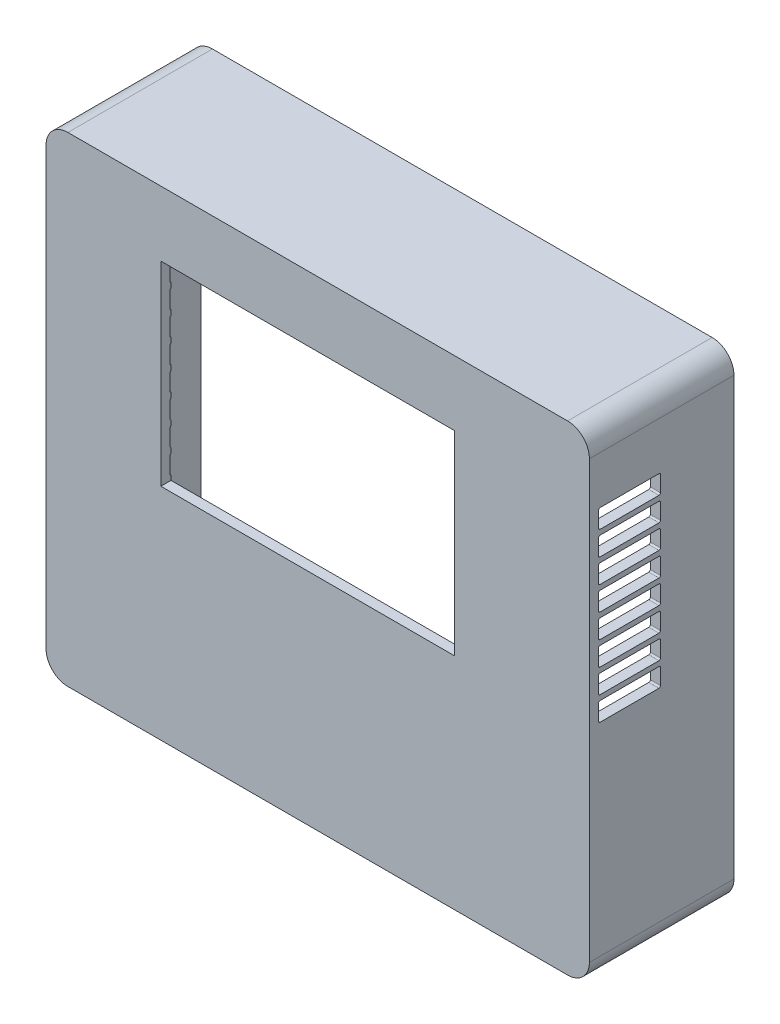
SolidWorks part; units mm, degrees
ref_plane "Front Plane" through (0, 0, 0) normal (0, 0, 1) x (1, 0, 0)
ref_plane "Top Plane" through (0, 0, 0) normal (0, 1, 0) x (1, 0, 0)
ref_plane "Right Plane" through (0, 0, 0) normal (1, 0, 0) x (0, 0, -1)
sketch "Sketch1" plane through (0, 0, 0) normal (0, 0, 1) x (1, 0, 0)
  line L4 (84, 51.09) -> (-14.4, 51.09)
  line L5 (-18.7, 46.79) -> (-18.7, -39.11)
  line L6 (-14.4, -43.41) -> (84, -43.41)
  line L7 (88.3, -39.11) -> (88.3, 46.79)
  line L8 (84, 51.09) -> (-14.4, 51.09)
  line L9 (-18.7, 46.79) -> (-18.7, -39.11)
  line L10 (-14.4, -43.41) -> (84, -43.41)
  line L11 (88.3, -39.11) -> (88.3, 46.79)
  line L12 (61.7, -0.1) -> (61.7, 38.3)
  line L13 (61.7, 38.3) -> (3.9, 38.3)
  line L14 (3.9, 38.3) -> (3.9, -0.1)
  line L15 (3.9, -0.1) -> (61.7, -0.1)
  line L16 (61.7, -0.1) -> (61.7, 38.3)
  line L17 (61.7, 38.3) -> (3.9, 38.3)
  line L18 (3.9, 38.3) -> (3.9, -0.1)
  line L19 (3.9, -0.1) -> (61.7, -0.1)
  arc A4 (88.3, 46.79) -> (84, 51.09) centre (84, 46.79) ccw
  arc A5 (-14.4, 51.09) -> (-18.7, 46.79) centre (-14.4, 46.79) ccw
  arc A6 (-18.7, -39.11) -> (-14.4, -43.41) centre (-14.4, -39.11) ccw
  arc A7 (84, -43.41) -> (88.3, -39.11) centre (84, -39.11) ccw
  arc A8 (88.3, 46.79) -> (84, 51.09) centre (84, 46.79) ccw
  arc A9 (-14.4, 51.09) -> (-18.7, 46.79) centre (-14.4, 46.79) ccw
  arc A10 (-18.7, -39.11) -> (-14.4, -43.41) centre (-14.4, -39.11) ccw
  arc A11 (84, -43.41) -> (88.3, -39.11) centre (84, -39.11) ccw
  dimension "D1" = 0
  dimension "D2" = 0
extrude "Boss-Extrude2" add sketch "Sketch1" against normal blind 2
sketch "Sketch2" plane through (0, 0, 0) normal (0, 0, 1) x (1, 0, 0)
  line L4 (84, 51.09) -> (-14.4, 51.09)
  line L5 (-18.7, 46.79) -> (-18.7, -39.11)
  line L6 (-14.4, -43.41) -> (84, -43.41)
  line L7 (88.3, -39.11) -> (88.3, 46.79)
  line L8 (84, 51.09) -> (-14.4, 51.09)
  line L9 (-18.7, 46.79) -> (-18.7, -39.11)
  line L10 (-14.4, -43.41) -> (84, -43.41)
  line L11 (88.3, -39.11) -> (88.3, 46.79)
  line L16 (84, 49.09) -> (-14.4, 49.09)
  line L17 (-16.7, 46.79) -> (-16.7, -39.11)
  line L18 (-14.4, -41.41) -> (84, -41.41)
  line L19 (86.3, -39.11) -> (86.3, 46.79)
  line L20 (84, 49.09) -> (-14.4, 49.09)
  line L21 (-16.7, 46.79) -> (-16.7, -39.11)
  line L22 (-14.4, -41.41) -> (84, -41.41)
  line L23 (86.3, -39.11) -> (86.3, 46.79)
  arc A4 (88.3, 46.79) -> (84, 51.09) centre (84, 46.79) ccw
  arc A5 (-14.4, 51.09) -> (-18.7, 46.79) centre (-14.4, 46.79) ccw
  arc A6 (-18.7, -39.11) -> (-14.4, -43.41) centre (-14.4, -39.11) ccw
  arc A7 (84, -43.41) -> (88.3, -39.11) centre (84, -39.11) ccw
  arc A8 (88.3, 46.79) -> (84, 51.09) centre (84, 46.79) ccw
  arc A9 (-14.4, 51.09) -> (-18.7, 46.79) centre (-14.4, 46.79) ccw
  arc A10 (-18.7, -39.11) -> (-14.4, -43.41) centre (-14.4, -39.11) ccw
  arc A11 (84, -43.41) -> (88.3, -39.11) centre (84, -39.11) ccw
  arc A16 (86.3, 46.79) -> (84, 49.09) centre (84, 46.79) ccw
  arc A17 (-14.4, 49.09) -> (-16.7, 46.79) centre (-14.4, 46.79) ccw
  arc A18 (-16.7, -39.11) -> (-14.4, -41.41) centre (-14.4, -39.11) ccw
  arc A19 (84, -41.41) -> (86.3, -39.11) centre (84, -39.11) ccw
  arc A20 (86.3, 46.79) -> (84, 49.09) centre (84, 46.79) ccw
  arc A21 (-14.4, 49.09) -> (-16.7, 46.79) centre (-14.4, 46.79) ccw
  arc A22 (-16.7, -39.11) -> (-14.4, -41.41) centre (-14.4, -39.11) ccw
  arc A23 (84, -41.41) -> (86.3, -39.11) centre (84, -39.11) ccw
  dimension "D1" = 0
  dimension "D2" = 2
extrude "Boss-Extrude3" add sketch "Sketch2" against normal up to surface (28.466 mm away)
sketch "Sketch4" plane through (0, -43.41, 0) normal (0, -1, 0) x (1, 0, 0)
  line L0 (68.12, -28.296) -> (69.827, -28.296) construction
  line L1 (69.827, -28.296) -> (69.827, -14.646) construction
  line L2 (69.827, -14.646) -> (68.12, -14.646) construction
  line L3 (66.12, -28.296) -> (68.12, -28.296) construction
  line L4 (-13.85, -17.296) -> (-13.85, -28.296)
  line L5 (-13.85, -28.296) -> (-4.55, -28.296)
  line L6 (-4.55, -28.296) -> (-4.55, -17.296)
  line L7 (-4.55, -17.296) -> (-13.85, -17.296)
  line L8 (-13.85, -17.296) -> (-13.85, -28.296)
  line L9 (-13.85, -28.296) -> (-4.55, -28.296)
  line L10 (-4.55, -28.296) -> (-4.55, -17.296)
  line L11 (-4.55, -17.296) -> (-13.85, -17.296)
  line L12 (-1.288, -21.4098) -> (-1.288, -28.2198)
  line L13 (-1.288, -28.2198) -> (16.408, -28.2198)
  line L14 (16.408, -28.2198) -> (16.408, -21.4098)
  line L15 (16.408, -21.4098) -> (-1.288, -21.4098)
  line L16 (-1.288, -21.4098) -> (-1.288, -28.2198)
  line L17 (-1.288, -28.2198) -> (16.408, -28.2198)
  line L18 (16.408, -28.2198) -> (16.408, -21.4098)
  line L19 (16.408, -21.4098) -> (-1.288, -21.4098)
  line L20 (20.375, -11.3798) -> (20.375, -28.2198)
  line L21 (20.375, -28.2198) -> (34.425, -28.2198)
  line L22 (34.425, -28.2198) -> (34.425, -11.3798)
  line L23 (34.425, -11.3798) -> (20.375, -11.3798)
  line L24 (20.375, -11.3798) -> (20.375, -28.2198)
  line L25 (20.375, -28.2198) -> (34.425, -28.2198)
  line L26 (34.425, -28.2198) -> (34.425, -11.3798)
  line L27 (34.425, -11.3798) -> (20.375, -11.3798)
  line L28 (37.375, -11.3798) -> (37.375, -28.2198)
  line L29 (37.375, -28.2198) -> (51.425, -28.2198)
  line L30 (51.425, -28.2198) -> (51.425, -11.3798)
  line L31 (51.425, -11.3798) -> (37.375, -11.3798)
  line L32 (37.375, -11.3798) -> (37.375, -28.2198)
  line L33 (37.375, -28.2198) -> (51.425, -28.2198)
  line L34 (51.425, -28.2198) -> (51.425, -11.3798)
  line L35 (51.425, -11.3798) -> (37.375, -11.3798)
  line L36 (68.12, -14.646) -> (66.12, -14.646) construction
  line L37 (57.38, -28.296) -> (66.12, -28.296) construction
  line L38 (66.12, -14.646) -> (57.38, -14.646) construction
  line L39 (55.38, -28.296) -> (57.38, -28.296) construction
  line L40 (57.38, -14.646) -> (55.38, -14.646) construction
  line L41 (53.673, -14.646) -> (53.673, -28.296) construction
  line L42 (53.673, -28.296) -> (55.38, -28.296) construction
  line L43 (55.38, -14.646) -> (53.673, -14.646) construction
  line L44 (68.12, -28.296) -> (69.827, -28.296)
  line L45 (69.827, -28.296) -> (69.827, -14.646)
  line L46 (69.827, -14.646) -> (68.12, -14.646)
  line L47 (66.12, -28.296) -> (68.12, -28.296)
  line L48 (68.12, -14.646) -> (66.12, -14.646)
  line L49 (57.38, -28.296) -> (66.12, -28.296)
  line L50 (66.12, -14.646) -> (57.38, -14.646)
  line L51 (55.38, -28.296) -> (57.38, -28.296)
  line L52 (57.38, -14.646) -> (55.38, -14.646)
  line L53 (53.673, -14.646) -> (53.673, -28.296)
  line L54 (53.673, -28.296) -> (55.38, -28.296)
  line L55 (55.38, -14.646) -> (53.673, -14.646)
  line L60 (72.33, -24.7898) -> (72.33, -28.2198)
  line L61 (72.33, -28.2198) -> (81.22, -28.2198)
  line L62 (81.22, -28.2198) -> (81.22, -24.7898)
  line L63 (81.22, -24.7898) -> (72.33, -24.7898)
  line L64 (72.33, -24.7898) -> (72.33, -28.2198)
  line L65 (72.33, -28.2198) -> (81.22, -28.2198)
  line L66 (81.22, -28.2198) -> (81.22, -24.7898)
  line L67 (81.22, -24.7898) -> (72.33, -24.7898)
  dimension "D1" = 0
  dimension "D2" = 0
  dimension "D3" = 0
  dimension "D4" = 0
  dimension "D5" = 0
extrude "Cut-Extrude2" cut sketch "Sketch4" against normal blind 2
sketch "Sketch8" plane through (-18.7, 0, 0) normal (-1, 0, 0) x (0, 0, 1)
  line L0 (-2.1, 19.6) -> (-13.7, 19.6) construction
  line L1 (-1.8, 19.9) -> (-1.8, 23) construction
  line L2 (-1.8, 24.6) -> (-1.8, 27.7) construction
  line L4 (-2.1, 28) -> (-13.7, 28) construction
  line L5 (-2.1, 23.3) -> (-13.7, 23.3) construction
  line L6 (-2.1, 24.3) -> (-13.7, 24.3) construction
  line L7 (-2.1, 18.6) -> (-13.7, 18.6) construction
  line L8 (-14, 18.3) -> (-14, 15.2) construction
  line L9 (-1.8, 15.2) -> (-1.8, 18.3) construction
  line L10 (-2.1, 14.9) -> (-13.7, 14.9) construction
  line L11 (-14, 13.6) -> (-14, 10.5) construction
  line L12 (-1.8, 10.5) -> (-1.8, 13.6) construction
  line L13 (-2.1, 10.2) -> (-13.7, 10.2) construction
  line L14 (-2.1, 13.9) -> (-13.7, 13.9) construction
  line L15 (-1.8, 1.1) -> (-1.8, 4.2) construction
  line L16 (-14, 4.2) -> (-14, 1.1) construction
  line L17 (-14, 8.9) -> (-14, 5.8) construction
  line L18 (-14, 8.9348) -> (-14, 7.2012) construction
  line L19 (-2.1, 9.2) -> (-13.7, 9.2) construction
  line L20 (-1.8, 5.8) -> (-1.8, 8.9) construction
  line L21 (-2.1, 5.5) -> (-13.7, 5.5) construction
  line L22 (-2.1, 4.5) -> (-13.7, 4.5) construction
  line L23 (-2.1, 0.8) -> (-13.7, 0.8) construction
  line L24 (-1.8, 29.3) -> (-1.8, 32.4) construction
  line L25 (-13.7, 29) -> (-2.1, 29) construction
  line L26 (-14, 32.4) -> (-14, 29.3) construction
  line L27 (-14, 37.1) -> (-14, 34) construction
  line L28 (-2.1, 32.7) -> (-13.7, 32.7) construction
  line L29 (-13.7, 33.7) -> (-2.1, 33.7) construction
  line L30 (-1.8, 34) -> (-1.8, 37.1) construction
  line L31 (-2.1, 37.4) -> (-13.7, 37.4) construction
  line L32 (-2.1, 19.6) -> (-13.7, 19.6)
  line L33 (-1.8, 19.9) -> (-1.8, 23)
  line L34 (-1.8, 24.6) -> (-1.8, 27.7)
  line L35 (-14, 23) -> (-14, 19.9) construction
  line L36 (-2.1, 28) -> (-13.7, 28)
  line L37 (-2.1, 23.3) -> (-13.7, 23.3)
  line L38 (-2.1, 24.3) -> (-13.7, 24.3)
  line L39 (-2.1, 18.6) -> (-13.7, 18.6)
  line L40 (-14, 18.3) -> (-14, 15.2)
  line L41 (-1.8, 15.2) -> (-1.8, 18.3)
  line L42 (-2.1, 14.9) -> (-13.7, 14.9)
  line L43 (-14, 13.6) -> (-14, 10.5)
  line L44 (-1.8, 10.5) -> (-1.8, 13.6)
  line L45 (-2.1, 10.2) -> (-13.7, 10.2)
  line L46 (-2.1, 13.9) -> (-13.7, 13.9)
  line L47 (-1.8, 1.1) -> (-1.8, 4.2)
  line L48 (-14, 4.2) -> (-14, 1.1)
  line L49 (-14, 8.9) -> (-14, 5.8)
  line L50 (-14, 8.9348) -> (-14, 7.2012)
  line L51 (-2.1, 9.2) -> (-13.7, 9.2)
  line L52 (-1.8, 5.8) -> (-1.8, 8.9)
  line L53 (-2.1, 5.5) -> (-13.7, 5.5)
  line L54 (-2.1, 4.5) -> (-13.7, 4.5)
  line L55 (-2.1, 0.8) -> (-13.7, 0.8)
  line L56 (-1.8, 29.3) -> (-1.8, 32.4)
  line L57 (-13.7, 29) -> (-2.1, 29)
  line L58 (-14, 32.4) -> (-14, 29.3)
  line L59 (-14, 37.1) -> (-14, 34)
  line L60 (-2.1, 32.7) -> (-13.7, 32.7)
  line L61 (-13.7, 33.7) -> (-2.1, 33.7)
  line L62 (-1.8, 34) -> (-1.8, 37.1)
  line L63 (-2.1, 37.4) -> (-13.7, 37.4)
  line L65 (-14, 27.7) -> (-14, 24.6) construction
  line L66 (-14, 23) -> (-14, 19.9)
  line L68 (-14, 27.7) -> (-14, 24.6)
  arc A0 (-1.8, 23) -> (-2.1, 23.3) centre (-2.1, 23) ccw construction
  arc A1 (-2.1, 19.6) -> (-1.8, 19.9) centre (-2.1, 19.9) ccw construction
  arc A2 (-1.8, 27.7) -> (-2.1, 28) centre (-2.1, 27.7) ccw construction
  arc A3 (-14, 19.9) -> (-13.7, 19.6) centre (-13.7, 19.9) ccw construction
  arc A4 (-14, 24.6) -> (-13.7, 24.3) centre (-13.7, 24.6) ccw construction
  arc A5 (-13.7, 28) -> (-14, 27.7) centre (-13.7, 27.7) ccw construction
  arc A6 (-13.7, 23.3) -> (-14, 23) centre (-13.7, 23) ccw construction
  arc A7 (-2.1, 24.3) -> (-1.8, 24.6) centre (-2.1, 24.6) ccw construction
  arc A8 (-13.7, 18.6) -> (-14, 18.3) centre (-13.7, 18.3) ccw construction
  arc A9 (-1.8, 18.3) -> (-2.1, 18.6) centre (-2.1, 18.3) ccw construction
  arc A10 (-2.1, 14.9) -> (-1.8, 15.2) centre (-2.1, 15.2) ccw construction
  arc A11 (-14, 15.2) -> (-13.7, 14.9) centre (-13.7, 15.2) ccw construction
  arc A12 (-13.7, 13.9) -> (-14, 13.6) centre (-13.7, 13.6) ccw construction
  arc A13 (-14, 10.5) -> (-13.7, 10.2) centre (-13.7, 10.5) ccw construction
  arc A14 (-1.8, 13.6) -> (-2.1, 13.9) centre (-2.1, 13.6) ccw construction
  arc A15 (-2.1, 10.2) -> (-1.8, 10.5) centre (-2.1, 10.5) ccw construction
  arc A16 (-2.1, 0.8) -> (-1.8, 1.1) centre (-2.1, 1.1) ccw construction
  arc A17 (-14, 1.1) -> (-13.7, 0.8) centre (-13.7, 1.1) ccw construction
  arc A18 (-13.7, 4.5) -> (-14, 4.2) centre (-13.7, 4.2) ccw construction
  arc A19 (-1.8, 8.9) -> (-2.1, 9.2) centre (-2.1, 8.9) ccw construction
  arc A20 (-14, 5.8) -> (-13.7, 5.5) centre (-13.7, 5.8) ccw construction
  arc A21 (-13.7, 9.2) -> (-14, 8.9) centre (-13.7, 8.9) ccw construction
  arc A22 (-2.1, 5.5) -> (-1.8, 5.8) centre (-2.1, 5.8) ccw construction
  arc A23 (-1.8, 4.2) -> (-2.1, 4.5) centre (-2.1, 4.2) ccw construction
  arc A24 (-1.8, 32.4) -> (-2.1, 32.7) centre (-2.1, 32.4) ccw construction
  arc A25 (-2.1, 29) -> (-1.8, 29.3) centre (-2.1, 29.3) ccw construction
  arc A26 (-14, 29.3) -> (-13.7, 29) centre (-13.7, 29.3) ccw construction
  arc A27 (-13.7, 37.4) -> (-14, 37.1) centre (-13.7, 37.1) ccw construction
  arc A28 (-14, 34) -> (-13.7, 33.7) centre (-13.7, 34) ccw construction
  arc A29 (-13.7, 32.7) -> (-14, 32.4) centre (-13.7, 32.4) ccw construction
  arc A30 (-2.1, 33.7) -> (-1.8, 34) centre (-2.1, 34) ccw construction
  arc A31 (-1.8, 37.1) -> (-2.1, 37.4) centre (-2.1, 37.1) ccw construction
  arc A32 (-1.8, 23) -> (-2.1, 23.3) centre (-2.1, 23) ccw
  arc A33 (-2.1, 19.6) -> (-1.8, 19.9) centre (-2.1, 19.9) ccw
  arc A34 (-1.8, 27.7) -> (-2.1, 28) centre (-2.1, 27.7) ccw
  arc A35 (-14, 19.9) -> (-13.7, 19.6) centre (-13.7, 19.9) ccw
  arc A36 (-14, 24.6) -> (-13.7, 24.3) centre (-13.7, 24.6) ccw
  arc A37 (-13.7, 28) -> (-14, 27.7) centre (-13.7, 27.7) ccw
  arc A38 (-13.7, 23.3) -> (-14, 23) centre (-13.7, 23) ccw
  arc A39 (-2.1, 24.3) -> (-1.8, 24.6) centre (-2.1, 24.6) ccw
  arc A40 (-13.7, 18.6) -> (-14, 18.3) centre (-13.7, 18.3) ccw
  arc A41 (-1.8, 18.3) -> (-2.1, 18.6) centre (-2.1, 18.3) ccw
  arc A42 (-2.1, 14.9) -> (-1.8, 15.2) centre (-2.1, 15.2) ccw
  arc A43 (-14, 15.2) -> (-13.7, 14.9) centre (-13.7, 15.2) ccw
  arc A44 (-13.7, 13.9) -> (-14, 13.6) centre (-13.7, 13.6) ccw
  arc A45 (-14, 10.5) -> (-13.7, 10.2) centre (-13.7, 10.5) ccw
  arc A46 (-1.8, 13.6) -> (-2.1, 13.9) centre (-2.1, 13.6) ccw
  arc A47 (-2.1, 10.2) -> (-1.8, 10.5) centre (-2.1, 10.5) ccw
  arc A48 (-2.1, 0.8) -> (-1.8, 1.1) centre (-2.1, 1.1) ccw
  arc A49 (-14, 1.1) -> (-13.7, 0.8) centre (-13.7, 1.1) ccw
  arc A50 (-13.7, 4.5) -> (-14, 4.2) centre (-13.7, 4.2) ccw
  arc A51 (-1.8, 8.9) -> (-2.1, 9.2) centre (-2.1, 8.9) ccw
  arc A52 (-14, 5.8) -> (-13.7, 5.5) centre (-13.7, 5.8) ccw
  arc A53 (-13.7, 9.2) -> (-14, 8.9) centre (-13.7, 8.9) ccw
  arc A54 (-2.1, 5.5) -> (-1.8, 5.8) centre (-2.1, 5.8) ccw
  arc A55 (-1.8, 4.2) -> (-2.1, 4.5) centre (-2.1, 4.2) ccw
  arc A56 (-1.8, 32.4) -> (-2.1, 32.7) centre (-2.1, 32.4) ccw
  arc A57 (-2.1, 29) -> (-1.8, 29.3) centre (-2.1, 29.3) ccw
  arc A58 (-14, 29.3) -> (-13.7, 29) centre (-13.7, 29.3) ccw
  arc A59 (-13.7, 37.4) -> (-14, 37.1) centre (-13.7, 37.1) ccw
  arc A60 (-14, 34) -> (-13.7, 33.7) centre (-13.7, 34) ccw
  arc A61 (-13.7, 32.7) -> (-14, 32.4) centre (-13.7, 32.4) ccw
  arc A62 (-2.1, 33.7) -> (-1.8, 34) centre (-2.1, 34) ccw
  arc A63 (-1.8, 37.1) -> (-2.1, 37.4) centre (-2.1, 37.1) ccw
extrude "Cut-Extrude4" cut sketch "Sketch8" against normal through all contours L62 A63 L63 A59 L59 A60 L61 A62 | L60 A61 L58 A58 L57 A57 L56 A56 | L38 A39 L34 A34 L36 A37 L68 A36 | L37 A38 L66 A35 L32 A33 L33 A32 | L40 A43 L42 A42 L41 A41 L39 A40 | L53 A54 L52 A51 L51 A53 L49 A52 | L46 A44 L43 A45 L45 A47 L44 A46 | L54 A50 L48 A49 L55 A48 L47 A55
